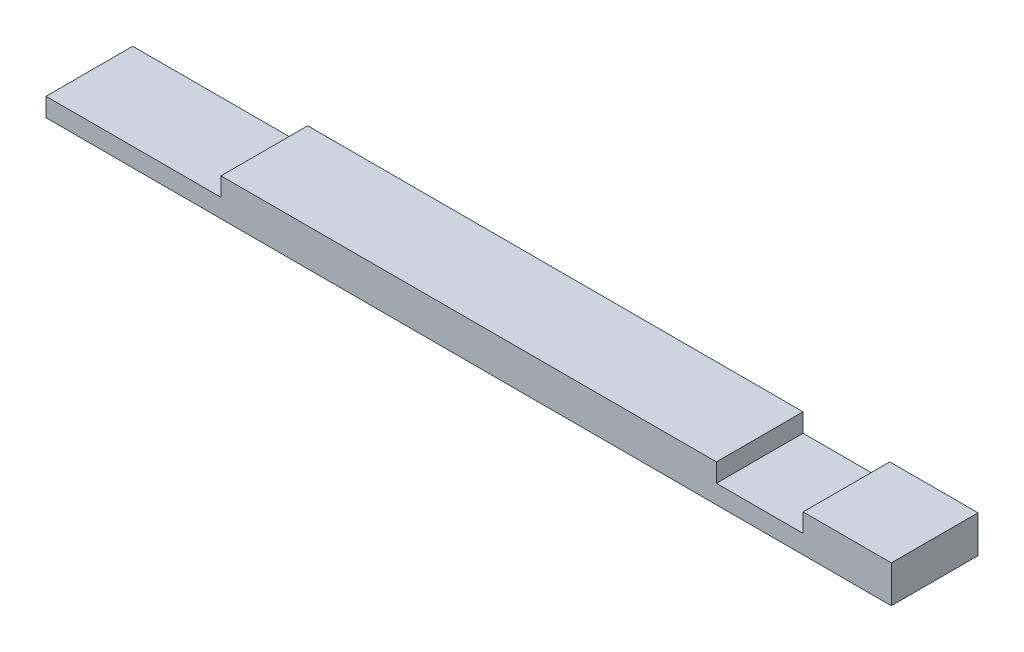
SolidWorks part; units mm, degrees
material "Pine"
ref_plane "Front Plane" through (0, 0, 0) normal (0, 0, 1) x (1, 0, 0)
ref_plane "Top Plane" through (0, 0, 0) normal (0, 1, 0) x (1, 0, 0)
ref_plane "Right Plane" through (0, 0, 0) normal (1, 0, 0) x (0, 0, -1)
sketch "Sketch1" plane through (0, 0, 0) normal (0, 1, 0) x (1, 0, 0)
  line L1 (0, 0) -> (866.775, 0)
  line L2 (0, 0) -> (0, 88.9)
  line L3 (0, 88.9) -> (866.775, 88.9)
  line L4 (866.775, 0) -> (866.775, 88.9)
  dimension "D1" = 88.9
  dimension "D2" = 866.775
extrude "Boss-Extrude1" add sketch "Sketch1" along normal blind 38.1
sketch "Sketch2" plane through (0, 38.1, 0) normal (0, 1, 0) x (1, 0, 0)
  line L0 (866.775, 88.9) -> (0, 88.9) construction
  line L1 (776.2875, 0) -> (687.3875, 0)
  line L2 (776.2875, 0) -> (776.2875, 88.9)
  line L3 (776.2875, 88.9) -> (687.3875, 88.9)
  line L4 (687.3875, 0) -> (687.3875, 88.9)
  line L5 (0, 0) -> (866.775, 0) construction
  line L6 (179.4002, 0) -> (0, 0)
  line L7 (179.4002, 0) -> (179.4002, 88.9)
  line L8 (179.4002, 88.9) -> (0, 88.9)
  line L9 (0, 0) -> (0, 88.9)
  line L13 (0, 88.9) -> (0, 0) construction
  point P13 (179.4002, 88.9)
  point P15 (776.2875, 44.45)
  point P16 (90.5002, 88.9)
  dimension "D1" = 179.4002
  dimension "D2" = 88.9
  dimension "D4" = 687.3875
extrude "Cut-Extrude1" cut sketch "Sketch2" against normal blind 19.05
